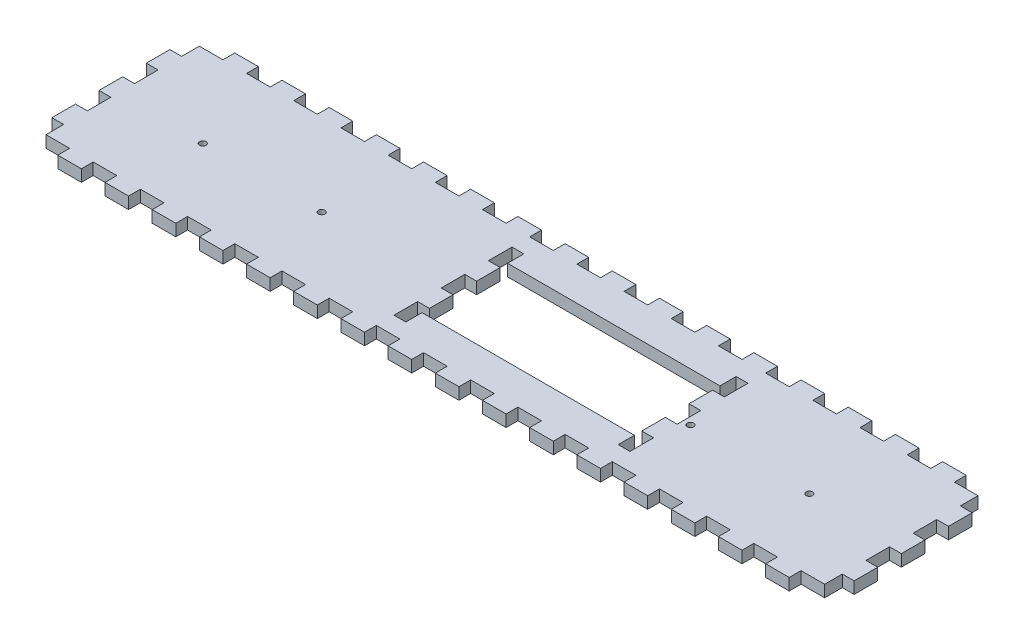
SolidWorks part; units mm, degrees
ref_plane "Front Plane" through (0, 0, 0) normal (0, 0, 1) x (1, 0, 0)
ref_plane "Top Plane" through (0, 0, 0) normal (0, 1, 0) x (1, 0, 0)
ref_plane "Right Plane" through (0, 0, 0) normal (1, 0, 0) x (0, 0, -1)
sketch "Sketch1" plane through (0, 0, 0) normal (0, 1, 0) x (1, 0, 0)
  line L1 (0, 0) -> (431.8, 0)
  line L2 (0, 0) -> (0, 95.25)
  line L3 (0, 95.25) -> (431.8, 95.25)
  line L4 (431.8, 0) -> (431.8, 95.25)
  dimension "D1" = 431.8
  dimension "D2" = 95.25
extrude "Boss-Extrude1" add sketch "Sketch1" along normal blind 6.35
sketch "Sketch2" plane through (0, 6.35, 0) normal (0, 1, 0) x (1, 0, 0)
  line L1 (431.8, 95.25) -> (0, 95.25) construction
  line L2 (6.35, 95.25) -> (19.05, 95.25)
  line L3 (6.35, 95.25) -> (6.35, 88.9)
  line L4 (6.35, 88.9) -> (19.05, 88.9)
  line L7 (19.05, 95.25) -> (19.05, 88.9)
  line L8 (0, 0) -> (431.8, 0) construction
  line L9 (6.35, 0) -> (19.05, 0)
  line L10 (6.35, 0) -> (6.35, 6.35)
  line L11 (6.35, 6.35) -> (19.05, 6.35)
  line L12 (19.05, 0) -> (19.05, 6.35)
  line L13 (0, 95.25) -> (0, 0) construction
  dimension "D1" = 6.35
  dimension "D2" = 12.7
  dimension "D3" = 6.35
extrude "Cut-Extrude1" cut sketch "Sketch2" against normal through all
pattern_linear "LPattern1" count 17 spacing 25.4 along (1, 0, 0) of "Cut-Extrude1"
sketch "Sketch3" plane through (0, 6.35, 0) normal (0, 1, 0) x (1, 0, 0)
  line L1 (6.35, 88.9) -> (0, 88.9)
  line L2 (6.35, 88.9) -> (6.35, 95.25)
  line L3 (6.35, 95.25) -> (0, 95.25)
  line L4 (0, 88.9) -> (0, 95.25)
  line L5 (6.35, 6.35) -> (0, 6.35)
  line L6 (6.35, 6.35) -> (6.35, 0)
  line L7 (6.35, 0) -> (0, 0)
  line L8 (0, 6.35) -> (0, 0)
  line L9 (425.45, 88.9) -> (431.8, 88.9)
  line L10 (425.45, 88.9) -> (425.45, 95.25)
  line L11 (425.45, 95.25) -> (431.8, 95.25)
  line L12 (431.8, 88.9) -> (431.8, 95.25)
  line L13 (425.45, 6.35) -> (431.8, 6.35)
  line L14 (425.45, 6.35) -> (425.45, 0)
  line L15 (425.45, 0) -> (431.8, 0)
  line L16 (431.8, 6.35) -> (431.8, 0)
extrude "Cut-Extrude2" cut sketch "Sketch3" against normal through all
sketch "Sketch5" plane through (0, 6.35, 0) normal (0, 1, 0) x (1, 0, 0)
  line L0 (311.15, 88.9) -> (311.15, 6.35) construction
  line L1 (190.5, 88.9) -> (190.5, 6.35) construction
  line L2 (184.15, 88.9) -> (196.85, 88.9) construction
  line L3 (196.85, 6.35) -> (184.15, 6.35) construction
  line L5 (190.5, 53.975) -> (184.15, 53.975)
  line L6 (190.5, 53.975) -> (190.5, 41.275)
  line L7 (190.5, 41.275) -> (184.15, 41.275)
  line L8 (184.15, 53.975) -> (184.15, 41.275)
  line L9 (311.15, 53.975) -> (304.8, 53.975)
  line L10 (311.15, 53.975) -> (311.15, 41.275)
  line L11 (311.15, 41.275) -> (304.8, 41.275)
  line L12 (304.8, 53.975) -> (304.8, 41.275)
  point P18 (190.5, 47.625)
  point P19 (311.15, 47.625)
  dimension "D1" = 6.35
  dimension "D2" = 12.7
extrude "Cut-Extrude4" cut sketch "Sketch5" against normal through all
pattern_linear "LPattern2" count 2 spacing 25.4 along (0, 0, -1) count 2 spacing 25.4 along (0, 0, 1) of "Cut-Extrude4"
sketch "Sketch6" plane through (0, 6.35, 0) normal (0, 1, 0) x (1, 0, 0)
  line L0 (190.5, 47.625) -> (304.8, 47.625) construction
  line L1 (190.5, 41.275) -> (190.5, 53.975) construction
  line L2 (304.8, 53.975) -> (304.8, 41.275) construction
  line L4 (304.8, 24.6063) -> (190.5, 24.6062)
  line L5 (304.8, 24.6063) -> (304.8, 70.6438)
  line L6 (304.8, 70.6438) -> (190.5, 70.6437)
  line L7 (190.5, 24.6062) -> (190.5, 70.6437)
  line L8 (304.8, 24.6063) -> (190.5, 70.6437) construction
  line L9 (304.8, 70.6438) -> (190.5, 24.6062) construction
  point P6 (247.65, 47.625)
  dimension "D1" = 46.0375
  dimension "D2" = 114.3
extrude "Cut-Extrude5" cut sketch "Sketch6" against normal through all
sketch "Sketch7" plane through (0, 6.35, 0) normal (0, 1, 0) x (1, 0, 0)
  line L0 (0, 44.45) -> (431.8, 44.45) construction
  line L1 (0, 88.9) -> (0, 6.35) construction
  line L2 (431.8, 6.35) -> (431.8, 88.9) construction
  line L3 (323.85, 0) -> (336.55, 0) construction
  circle A0 centre (52.65, 44.45) radius 1.75
  circle A1 centre (116.65, 44.45) radius 1.75
  circle A2 centre (315.15, 44.45) radius 1.75
  circle A3 centre (379.15, 44.45) radius 1.75
  dimension "D6" = 3.5
  dimension "D1" = 44.45
  dimension "D2" = 64
  dimension "D3" = 64
  dimension "D4" = 116.65
  dimension "D5" = 116.65
extrude "Cut-Extrude6" cut sketch "Sketch7" against normal through all
sketch "Sketch8" plane through (0, 6.35, 0) normal (0, 1, 0) x (1, 0, 0)
  line L0 (0, 88.9) -> (0, 6.35) construction
  line L1 (0, 88.9) -> (6.35, 88.9)
  line L2 (0, 88.9) -> (0, 79.375)
  line L3 (0, 79.375) -> (6.35, 79.375)
  line L4 (6.35, 88.9) -> (6.35, 79.375)
  line L5 (0, 6.35) -> (6.35, 6.35)
  line L6 (0, 6.35) -> (0, 15.875)
  line L7 (0, 15.875) -> (6.35, 15.875)
  line L8 (6.35, 6.35) -> (6.35, 15.875)
  line L9 (0, 28.575) -> (6.35, 28.575)
  line L10 (0, 28.575) -> (0, 41.275)
  line L11 (0, 41.275) -> (6.35, 41.275)
  line L12 (6.35, 28.575) -> (6.35, 41.275)
  line L13 (190.5, 53.975) -> (184.15, 53.975) construction
  line L14 (0, 66.675) -> (6.35, 66.675)
  line L15 (0, 66.675) -> (0, 53.975)
  line L16 (0, 53.975) -> (6.35, 53.975)
  line L17 (6.35, 66.675) -> (6.35, 53.975)
  line L18 (184.15, 41.275) -> (190.5, 41.275) construction
  line L19 (190.5, 28.575) -> (184.15, 28.575) construction
  line L20 (19.05, 0) -> (19.05, 6.35) construction
  line L21 (190.5, 79.375) -> (184.15, 79.375) construction
  line L22 (184.15, 15.875) -> (190.5, 15.875) construction
extrude "Cut-Extrude7" cut sketch "Sketch8" against normal through all
pattern_linear "LPattern3" count 2 spacing 425.45 along (1, 0, 0) of "Cut-Extrude7"
